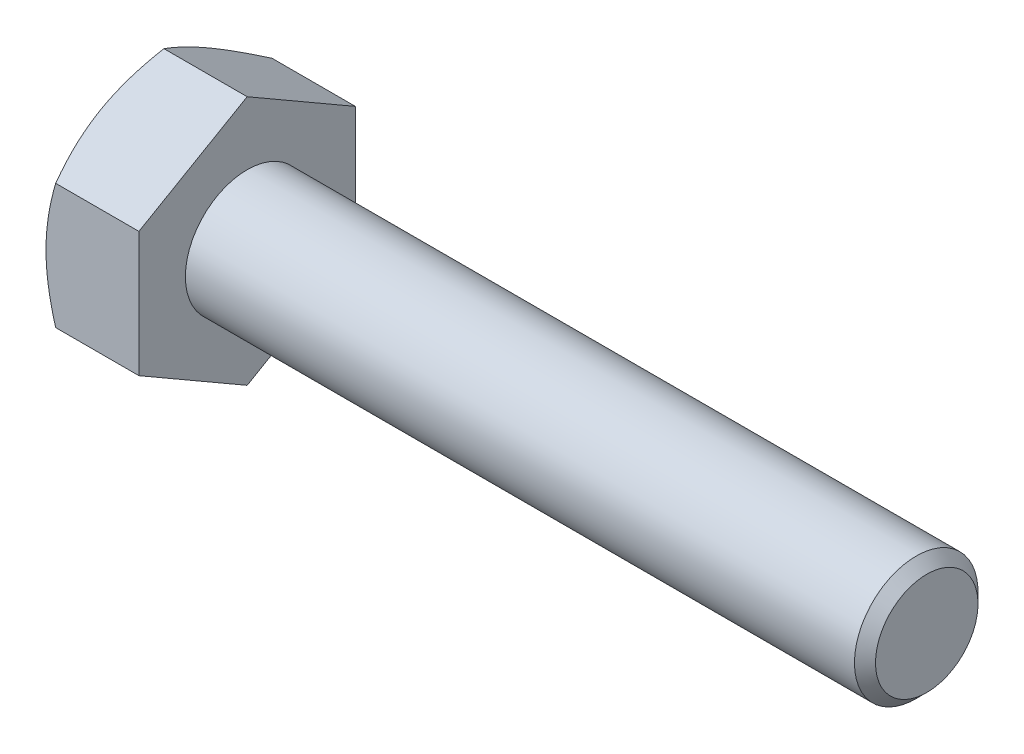
SolidWorks part; units mm, degrees
extrude "BaseHead" add sketch "Sketch1" along normal blind 4.7752
sketch "Sketch1" plane through (0, 0, 0) normal (1, 0, 0) x (0, 0, -1)
  line L0 (5.5626, 3.2116) -> (5.5626, -3.2116)
  line L1 (-5.5626, 3.2116) -> (-5.5626, -3.2116)
  line L2 (5.5626, -3.2116) -> (0, -6.4231)
  line L3 (0, -6.4231) -> (-5.5626, -3.2116)
  line L4 (5.5626, 3.2116) -> (0, 6.4231)
  line L5 (0, 6.4231) -> (-5.5626, 3.2116)
  dimension "Width_flats" = 11.1252
  dimension "D2" = 120
  dimension "D3" = 5.5626
  dimension "D4" = 5.5626
  dimension "D5" = 5.5626
ref_plane "Plane1" through (0, 0, 0) normal (0, 0, 1) x (1, 0, 0)
ref_plane "Plane2" through (0, 0, 0) normal (0, 1, 0) x (1, 0, 0)
ref_plane "Plane3" through (0, 0, 0) normal (1, 0, 0) x (0, 0, -1)
other "Configuration Table"
sketch "BodySke" plane through (0, 0, 0) normal (0, 0, 1) x (1, 0, 0)
  line L0 (0, 3.2116) -> (0, -3.2116) construction
  line L1 (0, 0) -> (39.7002, 0)
  line L2 (0, 0) -> (0, 3.175)
  line L3 (0, 3.175) -> (39.1592, 3.175)
  line L4 (39.7002, 0) -> (39.7002, 2.634)
  line L5 (4.7752, 6.4231) -> (4.7752, 3.2116) construction
  line L6 (39.7002, 2.634) -> (39.1592, 3.175)
  line L7 (0, 0) -> (96.52, 0) construction
  line L8 (39.7002, -2.634) -> (39.1592, -3.175) construction
  line L9 (0, -3.175) -> (39.1592, -3.175) construction
  line L10 (5.682, 15.24) -> (5.682, -2.54) construction
  line L11 (20.6502, 15.24) -> (20.6502, -2.54) construction
  line L12 (4.7752, 3.2116) -> (4.7752, -3.2116) construction
  dimension "Diameter" = 6.35
revolve "BaseBody" add sketch "BodySke" angle 360 about L7
cosmetic thread "ThreadCosmetic" parameters "Thread_length"=19.05, "Thread_minor"=5.268
sketch "Sketch3" plane through (0, 0, 0) normal (0, 0, 1) x (1, 0, 0)
  line L0 (0, 5.5626) -> (4.163, 12.7731)
  line L1 (0, 6.4231) -> (0, 3.2116) construction
  line L2 (4.163, 12.7731) -> (4.163, 19.1231)
  line L3 (4.163, 19.1231) -> (-12.7, 19.1231)
  line L4 (-12.7, 19.1231) -> (-12.7, 5.5626)
  line L5 (-12.7, 5.5626) -> (0, 5.5626)
  line L6 (0, 0) -> (99.06, 0) construction
  line L7 (4.7752, 6.4231) -> (0, 6.4231) construction
  dimension "D1" = 5.5626
  dimension "D2" = 6.35
  dimension "D3" = 12.7
  dimension "D4" = 6.35
  dimension "Head_ch_ang" = 30
revolve "HeadChamfer" cut sketch "Sketch3" angle 360 about L6
fillet "HeadFillet" [suppressed] radius 0.762
sketch "ThdSchSke" plane through (0, 0, 0) normal (0, 0, 1) x (1, 0, 0)
  line L0 (20.6502, -2.634) -> (20.2714, -3.175)
  line L1 (20.6502, -2.634) -> (21.029, -3.175)
  line L2 (21.029, -3.175) -> (21.029, -3.9688)
  line L3 (-3.175, 0) -> (5.1513, 0) construction
  line L5 (21.029, -3.9688) -> (20.2714, -3.9688)
  line L6 (20.2714, -3.9688) -> (20.2714, -3.175)
  dimension "Thread_minor" = 5.268
  dimension "Diameter" = 6.35
  dimension "Start" = 20.6502
revolve "ThreadSchematic" [suppressed] cut sketch "ThdSchSke" angle 360 about L3
pattern_linear "ThdSchPat" [suppressed]
equation "\"D3@Sketch1\" = \"Width_flats@Sketch1\" / 2"
equation "\"D4@Sketch1\" = \"D3@Sketch1\""
equation "\"D5@Sketch1\" = \"D4@Sketch1\""
equation "\"Thread_minor@ThreadCosmetic\" = \"Minor_dia@BodySke\""
equation "\"D1@Sketch3\" = \"Width_flats@Sketch1\" / 2"
equation "\"Thread_length@ThreadCosmetic\" = ((sgn( (\"Length@BodySke\" - \"Advance@BodySke\" ) - \"Thread_nom@BodySke\" )-1)*( (\"Length@BodySke\" - \"Advance@BodySke\" ) - \"Thread_nom@BodySke\" ))/-2+ \"Thread_nom@BodySke\""
equation "\"Thread_minor@ThdSchSke\" = \"Minor_dia@BodySke\""
equation "\"Diameter@ThdSchSke\" = \"Diameter@BodySke\""
equation "\"Overcut@ThdSchSke\" = \"Diameter@BodySke\" * 1.25"
equation "\"Start@ThdSchSke\" = \"Head_ht@BaseHead\" + \"Length@BodySke\" - \"Thread_length@ThreadCosmetic\"  '---Non-countersunk---"
equation "\"Num_threads@ThdSchPat\" = int( \"Thread_length@ThreadCosmetic\" / \"Advance@BodySke\" + 0.999 )  + 1"
equation "\"Advance@ThdSchPat\" = \"Thread_length@ThreadCosmetic\" /  (\"Num_threads@ThdSchPat\" - 1) 'relax it"
equation "\"Num_threads@ThdSchPat\" = \"Num_threads@ThdSchPat\" - sgn( \"Num_threads@ThdSchPat\" - 1) '---chamfered tips only---"
